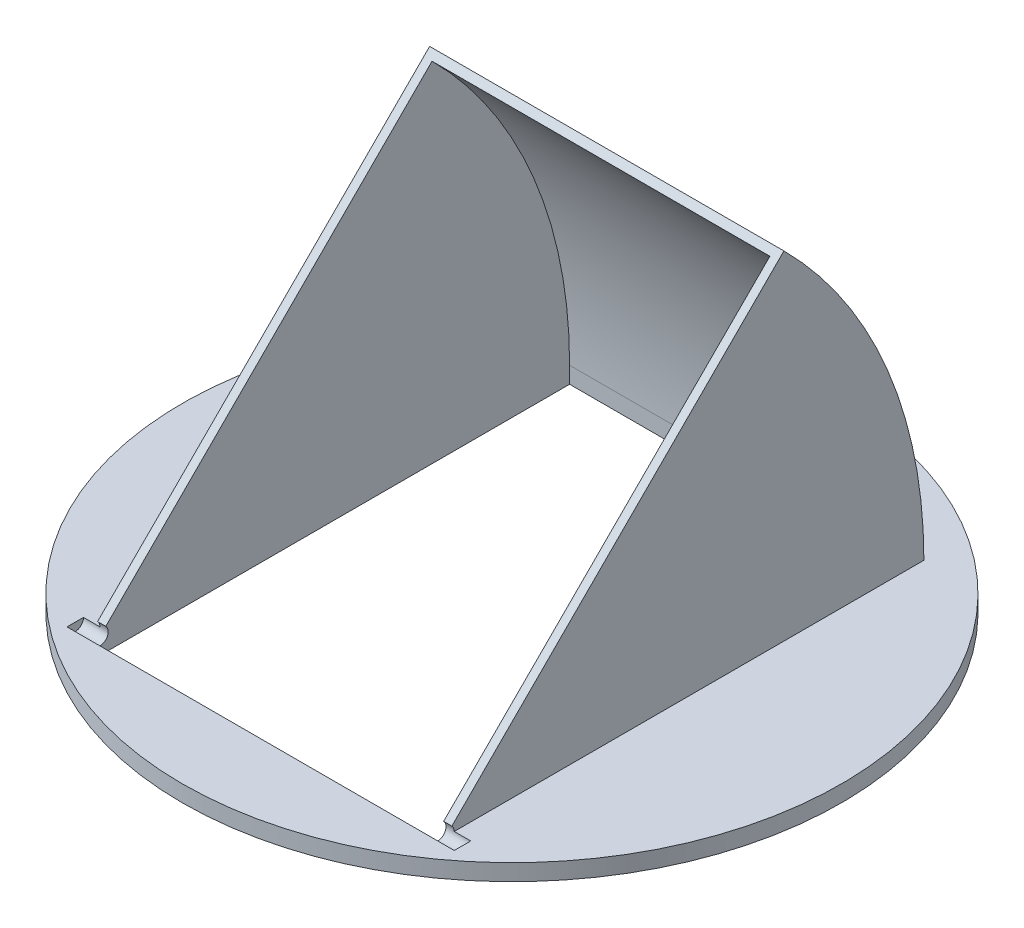
SolidWorks part; units mm, degrees
ref_plane "Front Plane" through (0, 0, 0) normal (0, 0, 1) x (1, 0, 0)
ref_plane "Top Plane" through (0, 0, 0) normal (0, 1, 0) x (1, 0, 0)
ref_plane "Right Plane" through (0, 0, 0) normal (1, 0, 0) x (0, 0, -1)
sketch "Sketch1" plane through (0, 0, 0) normal (0, 1, 0) x (1, 0, 0)
  circle A0 centre (0, 0) radius 127
  dimension "D1" = 254
extrude "Boss-Extrude1" add sketch "Sketch1" along normal blind 6.35
sketch "Sketch2" plane through (0, 6.35, 0) normal (0, 1, 0) x (1, 0, 0)
  line L0 (-68.2625, -93.6625) -> (-68.2625, 93.6625)
  line L1 (65.0875, -90.4875) -> (-65.0875, -90.4875)
  line L2 (65.0875, -90.4875) -> (65.0875, 90.4875)
  line L3 (65.0875, 90.4875) -> (-65.0875, 90.4875)
  line L4 (-65.0875, -90.4875) -> (-65.0875, 90.4875)
  line L5 (65.0875, -90.4875) -> (-65.0875, 90.4875) construction
  line L6 (65.0875, 90.4875) -> (-65.0875, -90.4875) construction
  line L7 (68.2625, 93.6625) -> (-68.2625, 93.6625)
  line L8 (68.2625, -93.6625) -> (68.2625, 93.6625)
  line L9 (68.2625, -93.6625) -> (-68.2625, -93.6625)
  point P0 (0, 0)
  dimension "D1" = 180.975
  dimension "D2" = 130.175
  dimension "D3" = 3.175
extrude "Boss-Extrude2" add sketch "Sketch2" along normal blind 180.975
sketch "Sketch3" plane through (68.2625, 0, 0) normal (1, 0, 0) x (0, 0, -1)
  line L0 (-93.6625, 187.325) -> (93.6625, 187.325)
  line L1 (93.6625, 187.325) -> (93.6625, 6.35)
  line L2 (93.6625, 6.35) -> (87.3125, 6.35)
  arc A0 (87.3125, 6.35) -> (-93.6625, 187.325) centre (-93.6625, 6.35) ccw
extrude "Cut-Extrude1" cut sketch "Sketch3" against normal up to next
sketch "Sketch6" plane through (0, 0, 93.6625) normal (0, 0, 1) x (1, 0, 0)
  line L22 (65.0875, 187.325) -> (65.0875, 6.35)
  line L23 (65.0875, 187.325) -> (65.0875, 6.35)
  line L24 (65.0875, 187.325) -> (-65.0875, 187.325)
  line L25 (-65.0875, 187.325) -> (-65.0875, 6.35)
  line L26 (-65.0875, 187.325) -> (-65.0875, 6.35)
  line L27 (-65.0875, 6.35) -> (65.0875, 6.35)
  dimension "D1" = 3.175
  dimension "D2" = 3.175
extrude "Cut-Extrude2" cut sketch "Sketch6" against normal up to next
sketch "Sketch7" plane through (0, 6.35, 0) normal (0, 1, 0) x (1, 0, 0)
  line L1 (-65.0875, -93.6625) -> (65.0875, -93.6625)
  line L2 (-65.0875, -93.6625) -> (-65.0875, 87.3125)
  line L3 (-65.0875, 87.3125) -> (65.0875, 87.3125)
  line L4 (65.0875, -93.6625) -> (65.0875, 87.3125)
extrude "Cut-Extrude3" cut sketch "Sketch7" against normal up to next
sketch "Sketch10" plane through (68.2625, 0, 0) normal (1, 0, 0) x (0, 0, -1)
  line L0 (-93.6625, 187.325) -> (-93.6625, 190.5)
  line L1 (87.3125, 6.35) -> (90.4875, 6.35)
  arc A1 (87.3125, 6.35) -> (-93.6625, 187.325) centre (-93.6625, 6.35) ccw construction
  arc A2 (90.4875, 6.35) -> (-93.6625, 190.5) centre (-93.6625, 6.35) ccw
  arc A3 (90.4875, 6.35) -> (-93.6625, 190.5) centre (-93.6625, 6.35) ccw
  arc A4 (-93.6625, 187.325) -> (87.3125, 6.35) centre (-93.6625, 6.35) cw
  dimension "D1" = 3.175
extrude "Boss-Extrude3" add sketch "Sketch10" against normal blind 136.525 contours A3 L0 A4 L1
sketch "Sketch12" plane through (68.2625, 0, 0) normal (1, 0, 0) x (0, 0, -1)
  line L0 (-93.6625, 6.35) -> (36.5512, 136.5637) construction
  line L1 (-93.6625, 6.35) -> (36.5512, 136.5637)
  line L2 (-93.6625, 6.35) -> (-93.6625, 190.5)
  arc A0 (90.4875, 6.35) -> (-93.6625, 190.5) centre (-93.6625, 6.35) ccw construction
  arc A1 (-93.6625, 190.5) -> (36.5512, 136.5637) centre (-93.6625, 6.35) cw
extrude "Cut-Extrude4" cut sketch "Sketch12" against normal blind 136.525
sketch "Sketch14" plane through (68.2625, 0, 0) normal (1, 0, 0) x (0, 0, -1)
sketch "Sketch15" plane through (68.2625, 0, 0) normal (1, 0, 0) x (0, 0, -1)
  circle A0 centre (-93.6625, 6.35) radius 3.175
extrude "Cut-Extrude5" cut sketch "Sketch15" against normal blind 142.875 and the other way blind 6.35
